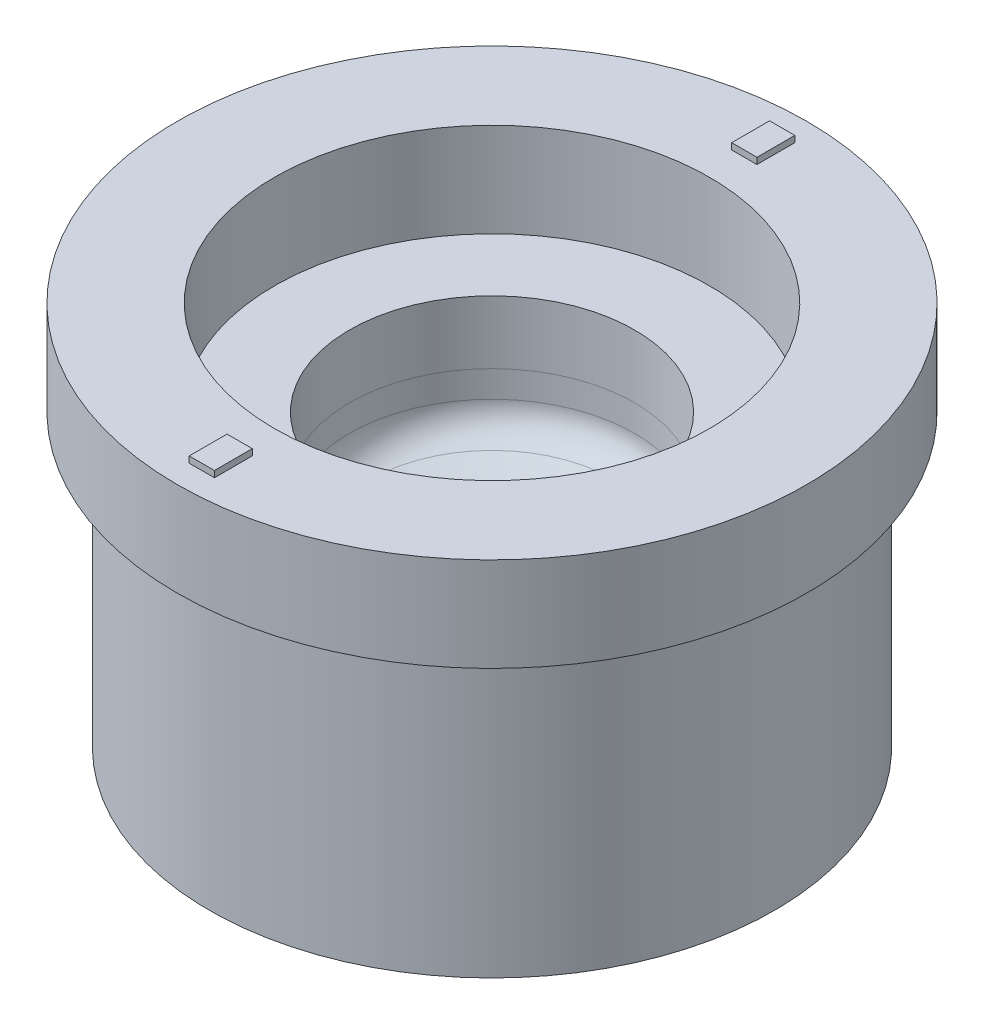
SolidWorks part; units mm, degrees
material "Galvanized Steel"
ref_plane "Front Plane" through (0, 0, 0) normal (0, 0, 1) x (1, 0, 0)
ref_plane "Top Plane" through (0, 0, 0) normal (0, 1, 0) x (1, 0, 0)
ref_plane "Right Plane" through (0, 0, 0) normal (1, 0, 0) x (0, 0, -1)
sketch "Sketch3" plane through (0, 0, 0) normal (0, 0, 1) x (1, 0, 0)
  line L0 (0, -20) -> (0, 0) construction
  line L1 (0, 0) -> (44.79, 0)
  line L2 (0, 0) -> (0, 46)
  line L3 (0, 46) -> (44.79, 46)
  line L4 (44.79, 0) -> (44.79, 46)
  dimension "D1" = 44.79
  dimension "D2" = 46
  dimension "D3" = 20
revolve "Revolve1" add sketch "Sketch3" angle 360 about L0
sketch "Sketch4" plane through (0, 46, 0) normal (0, 1, 0) x (1, 0, 0)
  circle A0 centre (0, 0) radius 22.6
  dimension "D1" = 45.2
extrude "Cut-Extrude1" cut sketch "Sketch4" against normal blind 10
sketch "Sketch5" plane through (0, 46, 0) normal (0, 1, 0) x (1, 0, 0)
  circle A0 centre (0, 0) radius 35
  circle A1 centre (0, 0) radius 37
  dimension "D2" = 70
  dimension "D1" = 2
extrude "Cut-Extrude3" cut sketch "Sketch5" against normal blind 10
ref_plane "Plane1" through (0, 61, 0) normal (0, 1, 0) x (1, 0, 0)
sketch "Sketch6" plane through (0, 61, 0) normal (0, 1, 0) x (1, 0, 0)
  circle A0 centre (0, 0) radius 49.89
  circle A1 centre (0, 0) radius 32.5 construction
  circle A2 centre (0, 0) radius 34.5
  dimension "D1" = 65
  dimension "D3" = 99.78
  dimension "D2" = 2
extrude "Boss-Extrude2" add sketch "Sketch6" against normal offset from surface (14.9 mm away) 0.1 separate body contours A0 | A2 up to face at (0, 46, 37)
sketch "Sketch13" plane through (0, 0, 0) normal (0, 0, 1) x (1, 0, 0)
  line L0 (0, 42.3889) -> (0, 8.4574) construction
  line L1 (0, 36) -> (-22.6038, 36)
  line L2 (22.6, 36) -> (-22.6, 36) construction
  line L3 (35, 36) -> (-35, 36) construction
  line L4 (-22.6038, 36) -> (-22.6038, 31.8)
  line L5 (-19.3139, 27.1015) -> (-1.342, 20.5603)
  line L6 (0, 21.5) -> (0, 36)
  arc A0 (-22.6038, 31.8) -> (-19.3139, 27.1015) centre (-17.6038, 31.8) ccw
  arc A1 (-1.342, 20.5603) -> (0, 21.5) centre (-1, 21.5) ccw
  point P16 (0, 20.0719)
  dimension "D1" = 5
  dimension "D2" = 1
  dimension "D3" = 4.2
  dimension "D4" = 70
  dimension "D5" = 14.5
revolve "Cut-Revolve1" cut sketch "Sketch13" angle 360 about L0
sketch "Sketch15" plane through (0, 61, 0) normal (0, 1, 0) x (1, 0, 0)
  line L1 (-2, -40) -> (2, -40)
  line L2 (-2, -40) -> (-2, -46)
  line L3 (-2, -46) -> (2, -46)
  line L4 (2, -40) -> (2, -46)
  point P4 (0, -40)
  dimension "D1" = 6
  dimension "D2" = 4
  dimension "D3" = 40
extrude "Boss-Extrude4" add sketch "Sketch15" along normal blind 1
pattern_circular "CirPattern2" count 2 over 360 about axis through (0, 0, 0) along (0, 1, 0) of "Boss-Extrude4"
